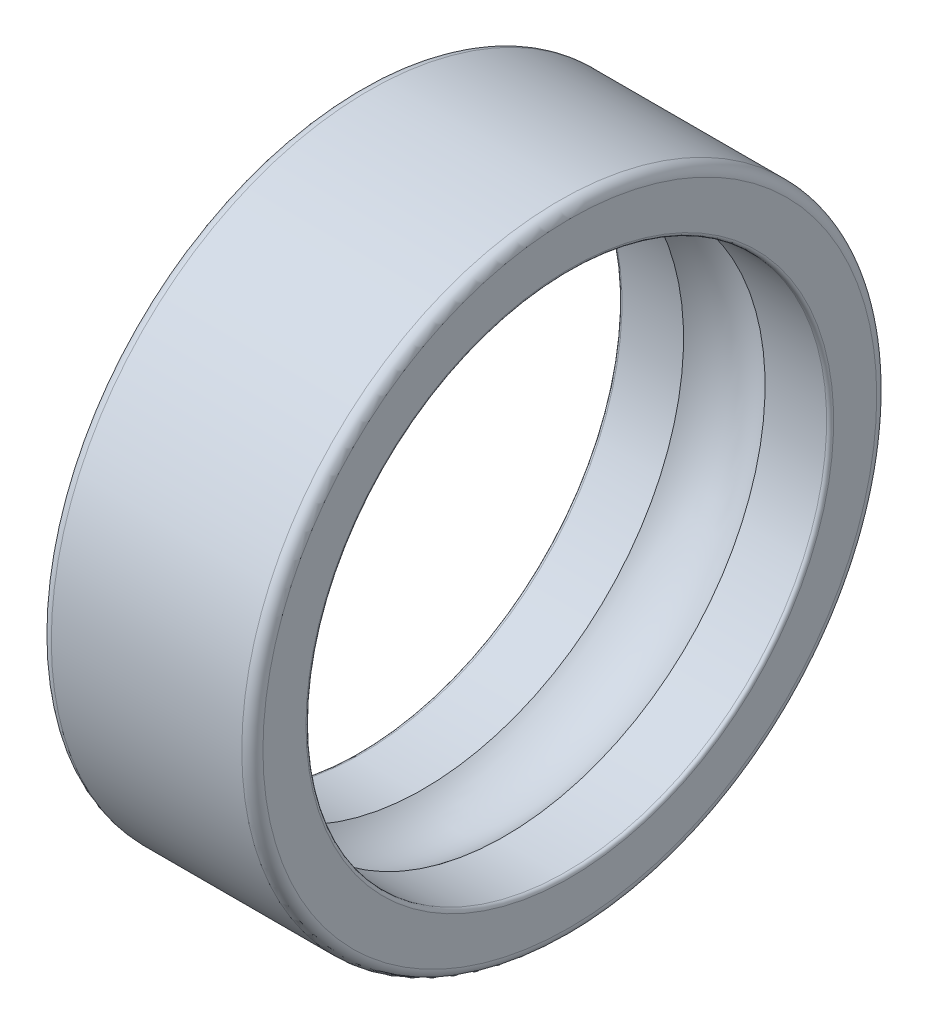
SolidWorks part; units mm, degrees
ref_plane "Front Plane" through (0, 0, 0) normal (0, 0, 1) x (1, 0, 0)
ref_plane "Top Plane" through (0, 0, 0) normal (0, 1, 0) x (1, 0, 0)
ref_plane "Right Plane" through (0, 0, 0) normal (1, 0, 0) x (0, 0, -1)
ref_plane "Plane1" through (0, 0, 0) normal (0, 0, 1) x (1, 0, 0)
sketch "Sketch1" plane through (0, 0, 0) normal (0, 0, 1) x (1, 0, 0)
  line L0 (0.0167, 1.23) -> (0.3074, 1.23)
  line L1 (0.6926, 1.23) -> (0.9833, 1.23)
  line L2 (1, 1.2467) -> (1, 1.45)
  line L3 (0.95, 1.5) -> (0.05, 1.5)
  line L4 (0, 1.45) -> (0, 1.2467)
  line L5 (1, 0) -> (-1, 0) construction
  arc A0 (0, 1.2467) -> (0.0167, 1.23) centre (0.0167, 1.2467) ccw
  arc A1 (0.3074, 1.23) -> (0.6926, 1.23) centre (0.5, 1) cw
  arc A2 (0.9833, 1.23) -> (1, 1.2467) centre (0.9833, 1.2467) ccw
  arc A3 (1, 1.45) -> (0.95, 1.5) centre (0.95, 1.45) ccw
  arc A4 (0.05, 1.5) -> (0, 1.45) centre (0.05, 1.45) ccw
revolve "Revolve1" add sketch "Sketch1" angle 360 about L5
